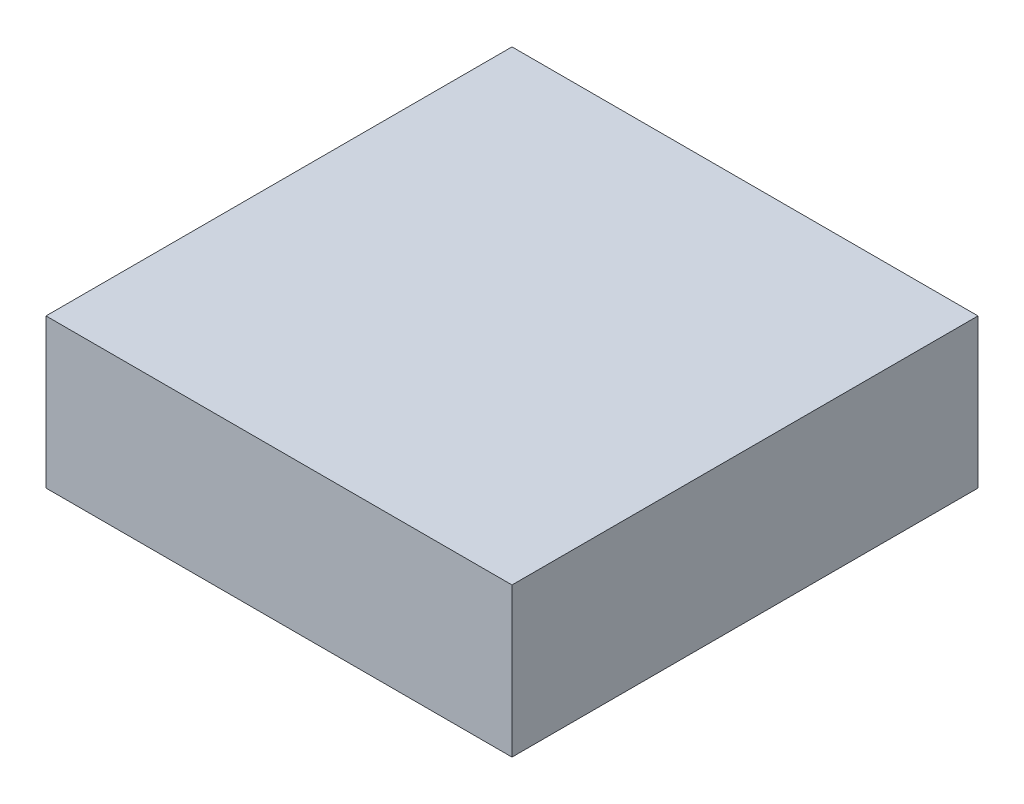
SolidWorks part; units mm, degrees
ref_plane "Front Plane" through (0, 0, 0) normal (0, 0, 1) x (1, 0, 0)
ref_plane "Top Plane" through (0, 0, 0) normal (0, 1, 0) x (1, 0, 0)
ref_plane "Right Plane" through (0, 0, 0) normal (1, 0, 0) x (0, 0, -1)
sketch "BaseS" plane through (0, 0, 0) normal (0, 1, 0) x (1, 0, 0)
  line L1 (-1.25, 1.25) -> (1.25, 1.25)
  line L2 (-1.25, 1.25) -> (-1.25, -1.25)
  line L3 (-1.25, -1.25) -> (1.25, -1.25)
  line L4 (1.25, 1.25) -> (1.25, -1.25)
  line L5 (-1.25, 1.25) -> (1.25, -1.25) construction
  line L6 (-1.25, -1.25) -> (1.25, 1.25) construction
  point P0 (0, 0)
  dimension "Width" = 2.5
  dimension "Length" = 2.5
extrude "Base" add sketch "BaseS" along normal blind 0.8
